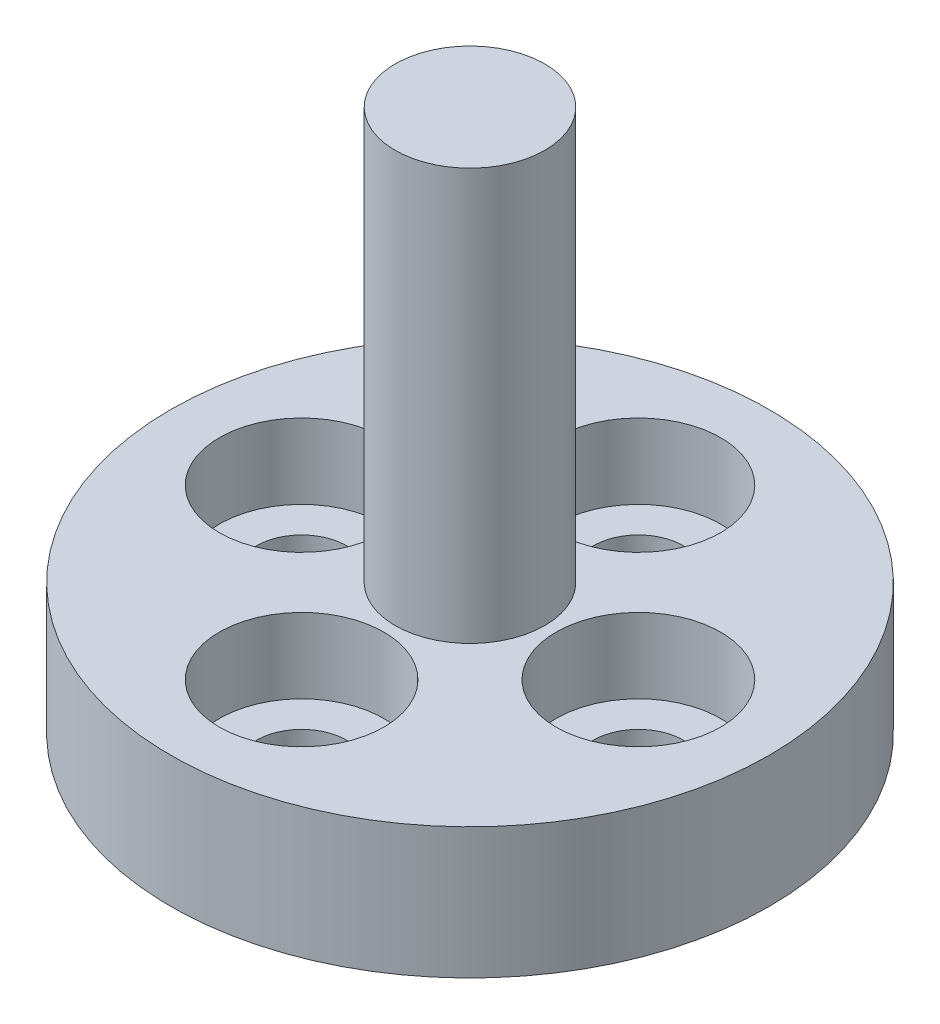
SolidWorks part; units mm, degrees
ref_plane "Front Plane" through (0, 0, 0) normal (0, 0, 1) x (1, 0, 0)
ref_plane "Top Plane" through (0, 0, 0) normal (0, 1, 0) x (1, 0, 0)
ref_plane "Right Plane" through (0, 0, 0) normal (1, 0, 0) x (0, 0, -1)
sketch "Sketch3" plane through (0, 0, 0) normal (0, 0, 1) x (1, 0, 0)
  line L0 (0, 0) -> (0, 14.5)
  line L1 (0, 14.5) -> (2, 14.5)
  line L2 (2, 14.5) -> (2, 3.5)
  line L3 (2, 3.5) -> (8, 3.5)
  line L4 (8, 3.5) -> (8, 0)
  line L5 (8, 0) -> (0, 0)
  dimension "D1" = 2
  dimension "D2" = 8
  dimension "D3" = 11
  dimension "D4" = 14.5
revolve "Revolve1" add sketch "Sketch3" angle 360 about L0
sketch "Sketch4" plane through (0, 3.5, 0) normal (0, 1, 0) x (1, 0, 0)
  circle A0 centre (0, 0) radius 4.5
  dimension "D1" = 9
sketch "Sketch7" plane through (0, 3.5, 0) normal (0, 1, 0) x (1, 0, 0)
  circle A0 centre (0, 0) radius 4.5 construction
  point P0 (-4.5, 0)
  point P4 (0, 4.5)
  point P6 (4.5, 0)
  point P8 (0, -4.5)
hole_wizard "CBORE for M2 SHCS1" positions "Sketch7" profile "Sketch6" counterbore size "M2" standard "ANSI Metric" end condition through all
sketch "Sketch6" plane through (-4.5, 3.5, 0) normal (1, 0, 0) x (0, 0, 1)
  line L0 (0, 0) -> (0, 3.5)
  line L1 (0, 3.5) -> (1.2, 3.5)
  line L3 (1.2, 3.5) -> (1.2, 2)
  line L4 (1.2, 2) -> (2.2, 2)
  line L5 (2.2, 2) -> (2.2, 0)
  line L7 (2.2, 0) -> (0, 0)
  line L11 (0, -6.35) -> (0, 107.95) construction
  dimension "Thru Hole Dia." = 2.4
  dimension "Thru Hole Depth" = 3.5
  dimension "C'Bore Dia." = 4.4
  dimension "C'Bore Depth" = 2
sketch "Sketch8" plane through (0, 0, 0) normal (0, -1, 0) x (1, 0, 0)
  circle A0 centre (0, 0) radius 1
  dimension "D1" = 2
extrude "Cut-Extrude1" cut sketch "Sketch8" against normal blind 14.06
fillet "Fillet1" radius 1 2 edges at (1, 0, 0) (1, 14.06, 0)
